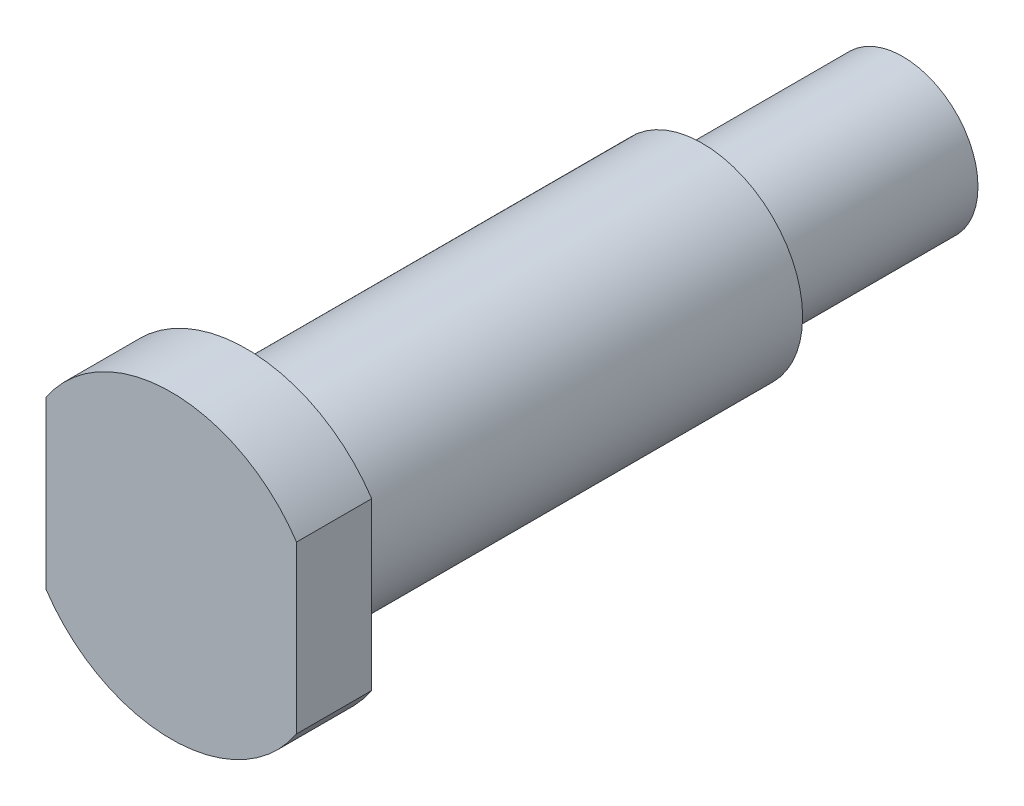
SolidWorks part; units mm, degrees
ref_plane "前视基准面" through (0, 0, 0) normal (0, 0, 1) x (1, 0, 0)
ref_plane "上视基准面" through (0, 0, 0) normal (0, 1, 0) x (1, 0, 0)
ref_plane "右视基准面" through (0, 0, 0) normal (1, 0, 0) x (0, 0, -1)
sketch "草图2" plane through (0, 0, 0) normal (1, 0, 0) x (0, 0, -1)
  line L0 (0, 0) -> (105.7683, 0) construction
  line L1 (0, 0) -> (0, 6)
  line L2 (0, 6) -> (3, 6)
  line L3 (3, 6) -> (3, 4)
  line L4 (3, 4) -> (21.2, 4)
  line L5 (21.2, 4) -> (21.2, 3)
  line L6 (0, 0) -> (29.2, 0)
  line L7 (21.2, 3) -> (29.2, 3)
  line L8 (29.2, 3) -> (29.2, 0)
  dimension "D1" = 12
  dimension "D2" = 18.2
  dimension "D3" = 3
  dimension "D4" = 8
  dimension "D5" = 6
  dimension "D6" = 8
revolve "旋转1" add sketch "草图2" angle 360 about L0
cosmetic thread "装饰螺纹线1" parameters "D2"=5
sketch "草图3" plane through (0, 0, 0) normal (0, 0, 1) x (1, 0, 0)
  line L1 (-5, -7.4895) -> (5, -7.4895)
  line L2 (-5, -7.4895) -> (-5, 7.4895)
  line L3 (-5, 7.4895) -> (5, 7.4895)
  line L4 (5, -7.4895) -> (5, 7.4895)
  line L5 (-5, -7.4895) -> (5, 7.4895) construction
  line L6 (-5, 7.4895) -> (5, -7.4895) construction
  point P0 (0, 0)
  dimension "D1" = 10
extrude "切除-拉伸1" cut sketch "草图3" against normal blind 10 flip side to cut
